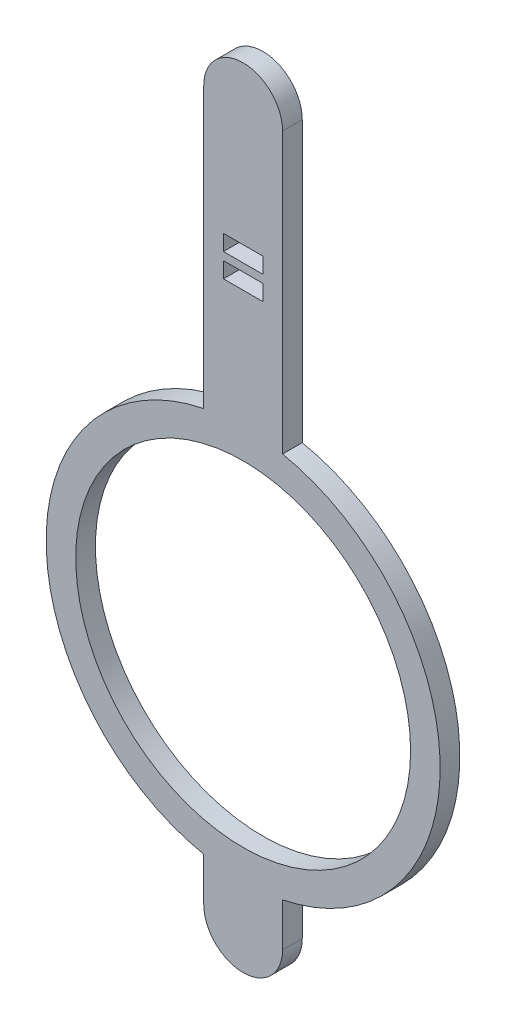
SolidWorks part; units mm, degrees
ref_plane "Front Plane" through (0, 0, 0) normal (0, 0, 1) x (1, 0, 0)
ref_plane "Top Plane" through (0, 0, 0) normal (0, 1, 0) x (1, 0, 0)
ref_plane "Right Plane" through (0, 0, 0) normal (1, 0, 0) x (0, 0, -1)
sketch "Croquis1" plane through (0, 0, 0) normal (0, 0, 1) x (1, 0, 0)
  line L2 (-0.5, -2.4495) -> (-0.5, -3)
  line L3 (0.5, -2.4495) -> (0.5, -3)
  line L4 (0, -5.2423) -> (0, 6) construction
  line L5 (-0.5, 2.4495) -> (-0.5, 6)
  line L6 (0.5, 2.4495) -> (0.5, 6)
  arc A0 (-2.1102, -0.25) -> (0, -2.125) centre (0, 0) ccw
  arc A1 (0.5, 6) -> (-0.5, 6) centre (0, 6) ccw
  arc A2 (-0.5, -3) -> (0.5, -3) centre (0, -3) ccw
  arc A3 (-0.5, 2.4495) -> (-0.5, -2.4495) centre (0, 0) ccw
  arc A4 (0.5, -2.4495) -> (0.5, 2.4495) centre (0, 0) ccw
  arc A5 (2.1102, -0.25) -> (0, 2.125) centre (0, 0) ccw
  arc A6 (0, 2.125) -> (-2.1102, -0.25) centre (0, 0) ccw
  arc A7 (0, -2.125) -> (2.1102, -0.25) centre (0, 0) ccw
  dimension "D1" = 5
  dimension "D8" = 4.25
  dimension "D3" = 1
  dimension "D6" = 3
  dimension "D7" = 6
extrude "Saliente-Extruir1" add sketch "Croquis1" along normal blind 0.25
sketch "Croquis2" plane through (0, 0, 0) normal (0, 0, -1) x (-1, 0, 0)
  line L1 (-0.25, 4.3) -> (0.25, 4.3)
  line L2 (-0.25, 4.3) -> (-0.25, 4.5)
  line L3 (-0.25, 4.5) -> (0.25, 4.5)
  line L4 (0.25, 4.3) -> (0.25, 4.5)
  line L5 (-0.25, 4.2) -> (0.25, 4.2)
  line L6 (-0.25, 4.2) -> (-0.25, 4)
  line L7 (-0.25, 4) -> (0.25, 4)
  line L8 (0.25, 4.2) -> (0.25, 4)
  point P8 (0, 4.5)
  dimension "D1" = 4
  dimension "D2" = 0.2
  dimension "D3" = 0.1
  dimension "D4" = 0.2
  dimension "D5" = 0.5
extrude "Cortar-Extruir1" cut sketch "Croquis2" against normal up to next
